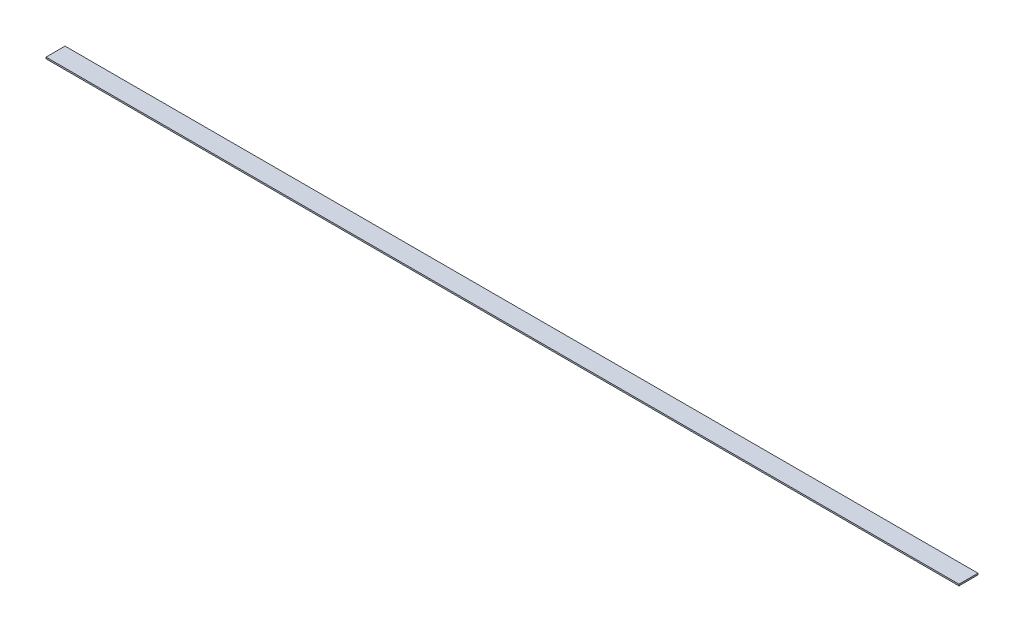
SolidWorks part; units mm, degrees
ref_plane "Front Plane" through (0, 0, 0) normal (0, 0, 1) x (1, 0, 0)
ref_plane "Top Plane" through (0, 0, 0) normal (0, 1, 0) x (1, 0, 0)
ref_plane "Right Plane" through (0, 0, 0) normal (1, 0, 0) x (0, 0, -1)
sketch "Sketch1" plane through (0, 0, 0) normal (0, 1, 0) x (1, 0, 0)
  line L1 (152.4, -3.175) -> (-152.4, -3.175)
  line L2 (152.4, -3.175) -> (152.4, 3.175)
  line L3 (152.4, 3.175) -> (-152.4, 3.175)
  line L4 (-152.4, -3.175) -> (-152.4, 3.175)
  line L5 (152.4, -3.175) -> (-152.4, 3.175) construction
  line L6 (152.4, 3.175) -> (-152.4, -3.175) construction
  point P0 (0, 0)
  dimension "D1" = 6.35
  dimension "D2" = 304.8
extrude "Boss-Extrude1" add sketch "Sketch1" along normal mid plane 0.5
